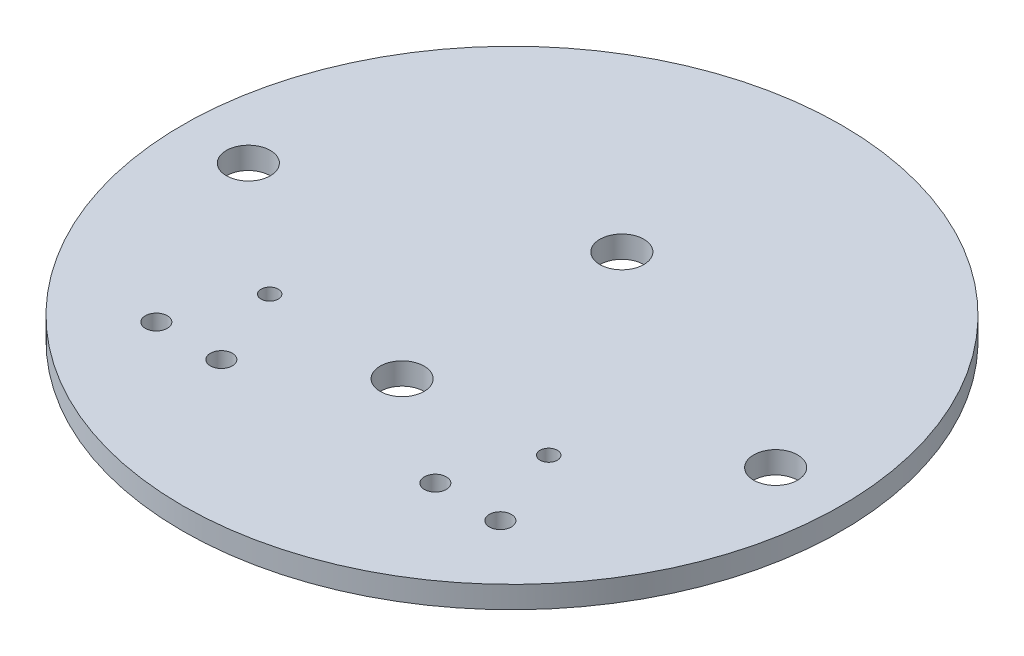
SolidWorks part; units mm, degrees
material "A-Glass Fiber"
ref_plane "Front Plane" through (0, 0, 0) normal (0, 0, 1) x (1, 0, 0)
ref_plane "Top Plane" through (0, 0, 0) normal (0, 1, 0) x (1, 0, 0)
ref_plane "Right Plane" through (0, 0, 0) normal (1, 0, 0) x (0, 0, -1)
sketch "Sketch1" plane through (0, 0, 0) normal (0, 1, 0) x (1, 0, 0)
  circle A0 centre (0, 0) radius 47.625
  dimension "D1" = 95.25
extrude "Boss-Extrude1" add sketch "Sketch1" along normal blind 3.175
extrude "Cut-Extrude1" cut sketch "Sketch2" against normal blind 263.398
sketch "Sketch2" plane through (-55.0397, 231.775, -116.0884) normal (0, 1, 0) x (-1, 0, 0)
  circle A0 centre (-93.1397, 116.0884) radius 3.175
  circle A1 centre (-16.9397, 116.0884) radius 3.175
extrude "Cut-Extrude2" cut sketch "Sketch3" against normal blind 25.4
sketch "Sketch3" plane through (-28.2644, -3.175, -82.3713) normal (0, -1, 0) x (1, 0, 0)
  circle A0 centre (28.2644, 98.2463) radius 3.175
  circle A1 centre (28.2644, 66.4963) radius 3.175
extrude "Cut-Extrude3" cut sketch "Sketch4" against normal blind 50.8
sketch "Sketch4" plane through (-28.2644, -3.175, -82.3713) normal (0, -1, 0) x (-1, 0, 0)
  circle A0 centre (-3.4041, -108.9143) radius 1.5875
  circle A1 centre (-12.8021, -108.9143) radius 1.5875
  circle A2 centre (-43.7266, -108.9143) radius 1.5875
  circle A3 centre (-53.1246, -108.9143) radius 1.5875
  circle A4 centre (-8.1031, -97.2303) radius 1.25
  circle A5 centre (-48.4256, -97.2303) radius 1.25
  point P8 (-3.4041, -105.7393)
  point P9 (-12.8021, -105.7393)
  point P12 (-43.7266, -105.7393)
  point P15 (-53.1246, -105.7393)
